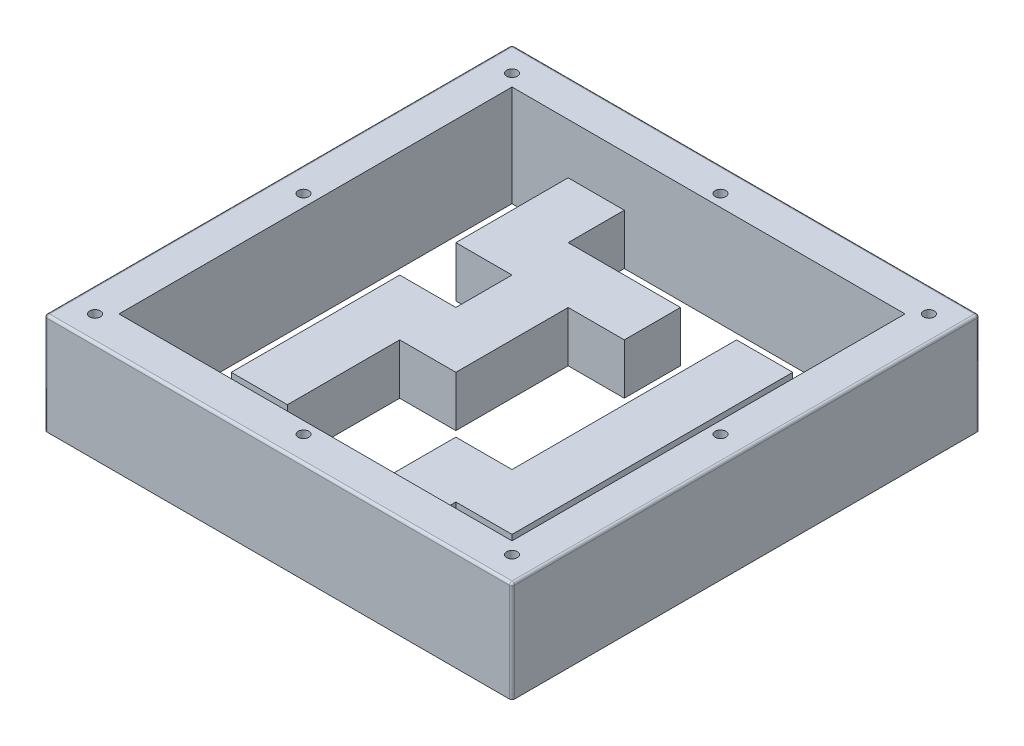
SolidWorks part; units mm, degrees
ref_plane "Plan de face" through (0, 0, 0) normal (0, 0, 1) x (1, 0, 0)
ref_plane "Plan de dessus" through (0, 0, 0) normal (0, 1, 0) x (1, 0, 0)
ref_plane "Plan de droite" through (0, 0, 0) normal (1, 0, 0) x (0, 0, -1)
sketch "Esquisse2" plane through (0, 0, 0) normal (0, 1, 0) x (1, 0, 0)
  line L1 (-92.5, 92.5) -> (92.5, 92.5)
  line L2 (-92.5, 92.5) -> (-92.5, -92.5)
  line L3 (-92.5, -92.5) -> (92.5, -92.5)
  line L4 (92.5, 92.5) -> (92.5, -92.5)
  dimension "D1" = 185
  dimension "D2" = 185
  dimension "D3" = 92.5
  dimension "D4" = 92.5
extrude "Boss.-Extru.1" add sketch "Esquisse2" against normal blind 3
sketch "Esquisse3" plane through (0, 0, 0) normal (0, 1, 0) x (1, 0, 0)
  line L0 (-77.77, 77.77) -> (77.77, 77.77)
  line L1 (-92.5, 92.5) -> (92.5, 92.5)
  line L2 (-92.5, 92.5) -> (-92.5, -92.5)
  line L3 (-92.5, -92.5) -> (92.5, -92.5)
  line L4 (92.5, 92.5) -> (92.5, -92.5)
  line L8 (77.77, 77.77) -> (77.77, -77.77)
  line L9 (-77.77, -77.77) -> (77.77, -77.77)
  line L10 (-77.77, 77.77) -> (-77.77, -77.77)
  dimension "D2" = 155.54
  dimension "D3" = 155.54
  dimension "D1" = 14.73
extrude "Boss.-Extru.2" add sketch "Esquisse3" along normal blind 40
sketch "Esquisse4" plane through (0, 0, 0) normal (0, 1, 0) x (1, 0, 0)
  line L0 (-55.55, 77.77) -> (-33.33, 77.77)
  line L1 (77.77, 77.77) -> (-77.77, 77.77) construction
  line L2 (-33.33, 77.77) -> (-33.33, 55.55)
  line L3 (-33.33, 55.55) -> (11.11, 55.55)
  line L4 (11.11, 55.55) -> (11.11, 33.33)
  line L5 (11.11, 33.33) -> (-11.11, 33.33)
  line L6 (-11.11, 33.33) -> (-11.11, -11.11)
  line L8 (-33.33, -11.11) -> (-33.33, -55.55)
  line L9 (-33.33, -55.55) -> (-55.55, -55.55)
  line L13 (-33.33, -11.11) -> (-11.11, -11.11)
  line L14 (-55.55, 77.77) -> (-55.55, 33.33)
  line L15 (-55.55, 33.33) -> (-33.33, 33.33)
  line L16 (-33.33, 33.33) -> (-33.33, 11.11)
  line L17 (-33.33, 11.11) -> (-55.55, 11.11)
  line L18 (-55.55, 11.11) -> (-55.55, -55.55)
  line L19 (-77.77, 77.77) -> (-77.77, -77.77) construction
  line L20 (-77.77, -77.77) -> (77.77, -77.77) construction
  line L21 (77.77, -77.77) -> (77.77, 77.77) construction
  line L22 (33.33, 55.55) -> (55.55, 55.55)
  line L23 (33.33, 55.55) -> (33.33, -33.33)
  line L25 (55.55, 55.55) -> (55.55, -55.55)
  line L28 (55.55, -55.55) -> (33.33, -55.55)
  line L30 (33.33, -33.33) -> (11.11, -33.33)
  line L32 (33.33, -77.77) -> (11.11, -77.77)
  line L33 (11.11, -33.33) -> (11.11, -77.77)
  line L34 (33.33, -55.55) -> (33.33, -77.77)
  line L35 (77.77, -77.77) -> (77.77, 77.77) construction
  dimension "D1" = 22.22
  dimension "D2" = 22.22
  dimension "D3" = 22.22
  dimension "D4" = 22.22
  dimension "D5" = 22.22
  dimension "D6" = 22.22
  dimension "D7" = 22.22
  dimension "D8" = 22.22
  dimension "D9" = 22.22
  dimension "D10" = 66.66
  dimension "D11" = 22.22
  dimension "D12" = 22.22
  dimension "D13" = 22.22
  dimension "D14" = 22.22
  dimension "D15" = 22.22
  dimension "D16" = 22.22
  dimension "D17" = 22.22
  dimension "D18" = 44.44
extrude "Boss.-Extru.3" add sketch "Esquisse4" along normal blind 20
sketch "Esquisse5" plane through (0, 0, 0) normal (0, 1, 0) x (1, 0, 0)
  line L0 (77.77, 77.77) -> (-33.33, 77.77) construction
  line L1 (-33.33, 55.55) -> (-11.11, 55.55)
  line L2 (-33.33, 55.55) -> (-33.33, 77.77)
  line L3 (-33.33, 77.77) -> (-11.11, 77.77)
  line L4 (-11.11, 55.55) -> (-11.11, 77.77)
  line L5 (-11.11, -11.11) -> (-11.11, 33.33) construction
  line L6 (-11.11, 33.33) -> (11.11, 33.33)
  line L7 (-11.11, 33.33) -> (-11.11, 11.11)
  line L8 (-11.11, 11.11) -> (11.11, 11.11)
  line L9 (11.11, 33.33) -> (11.11, 11.11)
  line L10 (11.11, 33.33) -> (11.11, 55.55) construction
  line L11 (-33.33, 11.11) -> (-55.55, 11.11) construction
  line L12 (33.33, -55.55) -> (55.55, -55.55) construction
  line L13 (-33.33, -11.11) -> (-20.98, -11.11)
  line L14 (-33.33, -11.11) -> (-33.33, -23.46)
  line L15 (-33.33, -23.46) -> (-20.98, -23.46)
  line L16 (-20.98, -11.11) -> (-20.98, -23.46)
  line L17 (-72.835, 28.395) -> (-60.485, 28.395)
  line L18 (-72.835, 28.395) -> (-72.835, 16.045)
  line L19 (-72.835, 16.045) -> (-60.485, 16.045)
  line L20 (-60.485, 28.395) -> (-60.485, 16.045)
  line L21 (-72.835, -60.485) -> (-60.485, -60.485)
  line L22 (-72.835, -60.485) -> (-72.835, -72.835)
  line L23 (-72.835, -72.835) -> (-60.485, -72.835)
  line L24 (-60.485, -60.485) -> (-60.485, -72.835)
  line L25 (60.485, -60.485) -> (72.835, -60.485)
  line L26 (60.485, -60.485) -> (60.485, -72.835)
  line L27 (60.485, -72.835) -> (72.835, -72.835)
  line L28 (72.835, -60.485) -> (72.835, -72.835)
  line L29 (11.11, -55.55) -> (-1.24, -55.55)
  line L30 (11.11, -55.55) -> (11.11, -43.2)
  line L31 (11.11, -43.2) -> (-1.24, -43.2)
  line L32 (-1.24, -55.55) -> (-1.24, -43.2)
  line L34 (11.11, -33.33) -> (11.11, -77.77) construction
  line L35 (-77.77, 77.77) -> (-77.77, -77.77) construction
  line L36 (-55.55, 33.33) -> (-33.33, 33.33) construction
  line L37 (-55.55, 77.77) -> (-55.55, 33.33) construction
  line L38 (-77.77, -77.77) -> (11.11, -77.77) construction
  line L39 (77.77, -77.77) -> (77.77, 77.77) construction
  dimension "D1" = 12.35
  dimension "D2" = 12.35
  dimension "D3" = 12.35
  dimension "D4" = 12.35
  dimension "D5" = 12.35
  dimension "D6" = 12.35
  dimension "D7" = 12.35
  dimension "D8" = 12.35
  dimension "D9" = 12.35
  dimension "D10" = 12.35
  dimension "D11" = 4.935
  dimension "D12" = 4.935
  dimension "D13" = 4.935
  dimension "D14" = 4.935
  dimension "D15" = 4.935
  dimension "D16" = 4.935
extrude "Enlèv. mat.-Extru.1" cut sketch "Esquisse5" against normal up to next
fillet "Congé1" radius 1 8 edges at (-92.5, 18.5, -92.5) (-92.5, 18.5, 92.5) (-92.5, 40, 0) (0, 40, 92.5) (0, 40, -92.5) (92.5, 40, 0) (92.5, 18.5, -92.5) (92.5, 18.5, 92.5)
sketch "Esquisse6" plane through (0, 40, 0) normal (0, 1, 0) x (1, 0, 0)
  line L0 (92.5, 91.5) -> (92.5, -91.5) construction
  line L1 (-91.5, 92.5) -> (91.5, 92.5) construction
  line L2 (91.5, -92.5) -> (-91.5, -92.5) construction
  line L3 (-92.5, -91.5) -> (-92.5, 91.5) construction
  circle A0 centre (-82.5, -82.5) radius 1.1
  circle A1 centre (82.5, -82.5) radius 1.1
  circle A2 centre (82.5, 82.5) radius 1.1
  circle A3 centre (-82.5, 82.5) radius 1.1
  circle A4 centre (0, 82.5) radius 1.1
  circle A5 centre (82.5, 0) radius 1.1
  circle A6 centre (-82.5, 0) radius 1.1
  circle A7 centre (0, -82.5) radius 1.1
  point P24 (0, 0)
  point P25 (0, 0)
  point P26 (0, 0)
  point P27 (0, 0)
  point P28 (0, 0)
  point P29 (0, 0)
  dimension "D1" = 2.2
  dimension "D2" = 10
  dimension "D3" = 10
  dimension "D4" = 10
  dimension "D5" = 10
  dimension "D6" = 82.5
  dimension "D7" = 82.5
  dimension "D8" = 82.5
extrude "Enlèv. mat.-Extru.2" cut sketch "Esquisse6" against normal through all
sketch "Esquisse7" plane through (0, 40, 0) normal (0, 1, 0) x (1, 0, 0)
  circle A0 centre (-82.5, -82.5) radius 2.1
  circle A1 centre (-82.5, 82.5) radius 2.1
  circle A2 centre (82.5, 82.5) radius 2.1
  circle A3 centre (82.5, -82.5) radius 2.1
  dimension "D1" = 4.2
extrude "Enlèv. mat.-Extru.3" cut sketch "Esquisse7" against normal blind 41
sketch "Esquisse8" plane through (0, 0, 92.5) normal (0, 0, 1) x (1, 0, 0)
  line L0 (-91.5, -3) -> (91.5, -3) construction
  line L1 (114.072, -20.4095) -> (-112.4133, -20.4095)
  line L2 (114.072, -20.4095) -> (114.072, 0)
  line L3 (114.072, 0) -> (-112.4133, 0)
  line L4 (-112.4133, -20.4095) -> (-112.4133, 0)
  dimension "D1" = 3
extrude "Enlèv. mat.-Extru.4" cut sketch "Esquisse8" against normal through all
sketch "Esquisse9" plane through (0, 40, 0) normal (0, 1, 0) x (1, 0, 0)
  circle A2 centre (0, 82.5) radius 2.1
  circle A3 centre (82.5, 0) radius 2.1
  circle A4 centre (0, -82.5) radius 2.1
  circle A5 centre (-82.5, 0) radius 2.1
  dimension "D1" = 4.2
extrude "Enlèv. mat.-Extru.5" cut sketch "Esquisse9" against normal blind 28
